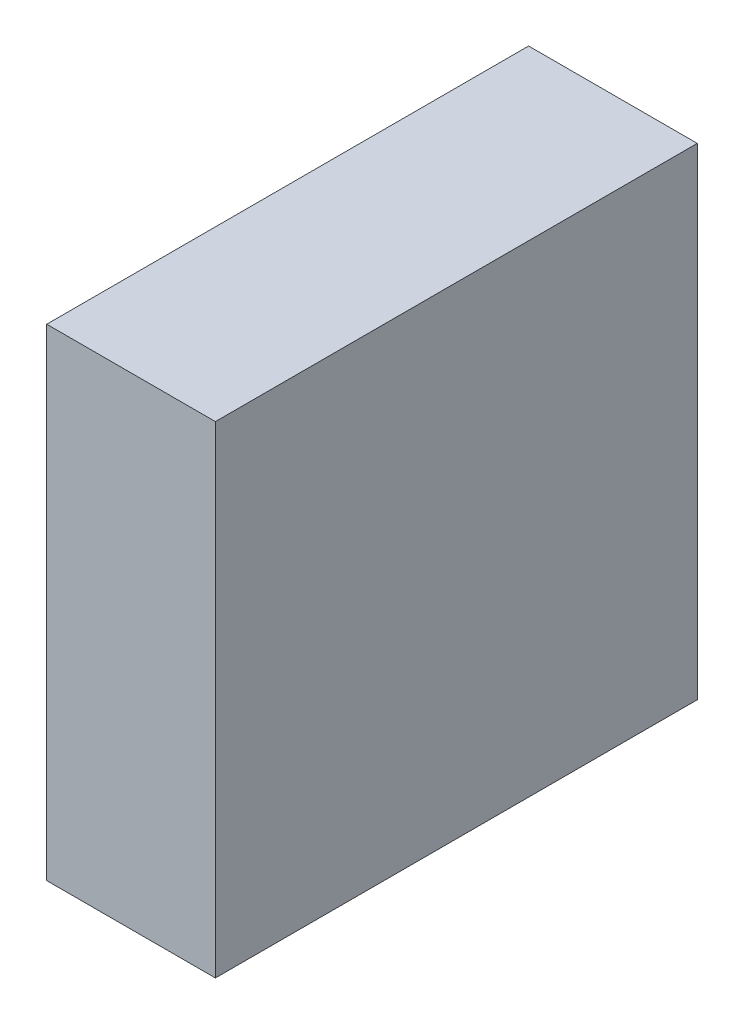
SolidWorks part; units mm, degrees
ref_plane "Front Plane" through (0, 0, 0) normal (1, 0, 0) x (0, 1, 0)
ref_plane "Top Plane" through (0, 0, 0) normal (0, 0, 1) x (0, 1, 0)
ref_plane "Right Plane" through (0, 0, 0) normal (0, 1, 0) x (-1, 0, 0)
sketch "Sketch1" plane through (0, 0, 0) normal (1, 0, 0) x (0, 1, 0)
  line L1 (20, 20) -> (-20, 20)
  line L2 (20, 20) -> (20, -20)
  line L3 (20, -20) -> (-20, -20)
  line L4 (-20, 20) -> (-20, -20)
  line L5 (20, 20) -> (-20, -20) construction
  line L6 (20, -20) -> (-20, 20) construction
  point P0 (0, 0)
  dimension "D1" = 40
  dimension "D2" = 40
extrude "Boss-Extrude1" add sketch "Sketch1" along normal blind 14
